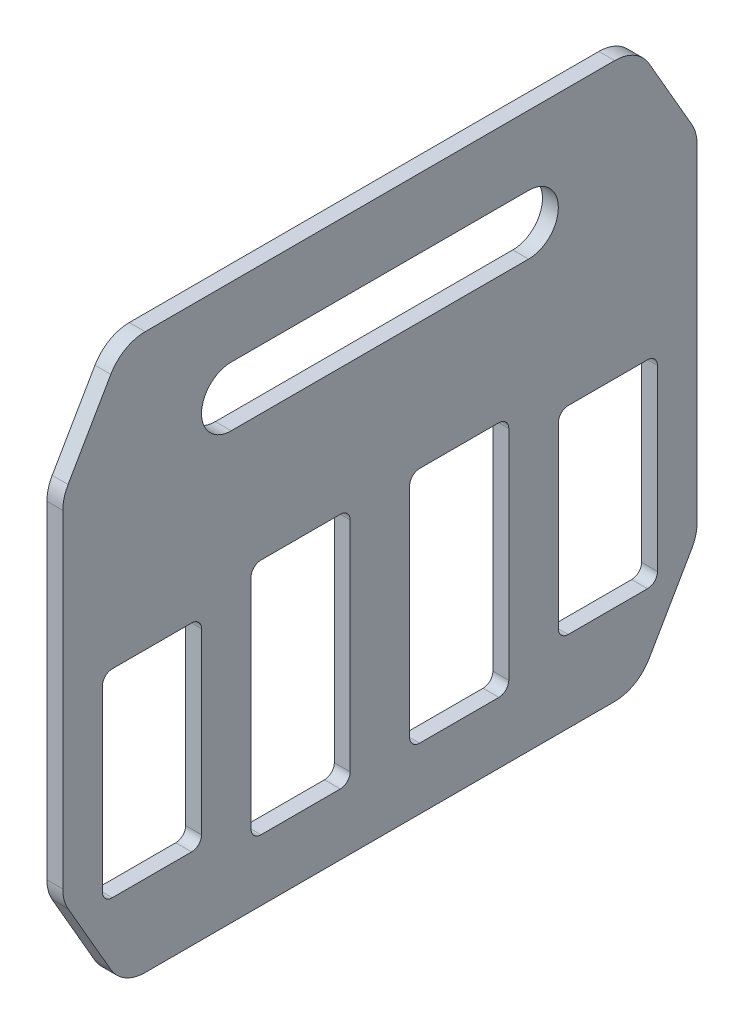
SolidWorks part; units mm, degrees
ref_plane "Front Plane" through (0, 0, 0) normal (0, 0, 1) x (1, 0, 0)
ref_plane "Top Plane" through (0, 0, 0) normal (0, 1, 0) x (1, 0, 0)
ref_plane "Right Plane" through (0, 0, 0) normal (1, 0, 0) x (0, 0, -1)
sketch "Sketch1" plane through (0, 0, 0) normal (1, 0, 0) x (0, 0, -1)
  line L0 (0, 254) -> (0, 0) construction
  line L2 (-203.2, 0) -> (-203.2, 254)
  line L4 (203.2, 0) -> (203.2, 254)
  line L5 (-95.25, 215.9) -> (95.25, 215.9) construction
  line L6 (-95.25, 234.95) -> (95.25, 234.95)
  line L7 (-95.25, 196.85) -> (95.25, 196.85)
  line L8 (-203.2, 127) -> (203.2, 127) construction
  line L15 (203.2, 0) -> (203.2, -76.2)
  line L16 (203.2, -76.2) -> (-203.2, -76.2)
  line L18 (-203.2, 0) -> (-203.2, -76.2)
  line L19 (-203.2, 254) -> (203.2, 254) construction
  line L36 (-203.2, 254) -> (-203.2, 279.4)
  line L37 (-203.2, 279.4) -> (203.2, 279.4)
  line L38 (203.2, 254) -> (203.2, 279.4)
  arc A0 (-95.25, 234.95) -> (-95.25, 196.85) centre (-95.25, 215.9) ccw
  arc A1 (95.25, 196.85) -> (95.25, 234.95) centre (95.25, 215.9) ccw
  point P10 (0, 215.9)
  dimension "D1" = 254
  dimension "D3" = 190.5
  dimension "D4" = 19.05
  dimension "D5" = 38.1
  dimension "D6" = 76.2
  dimension "D7" = 25.4
extrude "Boss-Extrude1" add sketch "Sketch1" along normal blind 10.16
sketch "Sketch2" plane through (0, 0, 0) normal (1, 0, 0) x (0, 0, -1)
  line L14 (-203.2, 127) -> (203.2, 127) construction
  line L15 (-196.85, 132.08) -> (-120.65, 132.08)
  line L16 (-196.85, 132.08) -> (-196.85, 121.92)
  line L17 (-196.85, 121.92) -> (-120.65, 121.92)
  line L18 (-120.65, 132.08) -> (-120.65, 121.92)
  line L19 (-203.2, 0) -> (-203.2, 254) construction
  line L20 (-38.1, 132.08) -> (38.1, 132.08)
  line L21 (-38.1, 132.08) -> (-38.1, 121.92)
  line L22 (38.1, 132.08) -> (38.1, 121.92)
  line L23 (-38.1, 121.92) -> (38.1, 121.92)
  line L24 (120.65, 132.08) -> (196.85, 132.08)
  line L25 (120.65, 132.08) -> (120.65, 121.92)
  line L26 (196.85, 132.08) -> (196.85, 121.92)
  line L27 (120.65, 121.92) -> (196.85, 121.92)
  point P6 (-196.85, 127)
  dimension "D1" = 6.35
  dimension "D2" = 10.16
  dimension "D3" = 76.2
  dimension "D4" = 3
extrude "Cut-Extrude1" cut sketch "Sketch2" along normal blind 4.572
chamfer "Chamfer1" distance 38.1 angle 60 4 edges at (5.08, -76.2, 203.2) (5.08, -76.2, -203.2) (5.08, 279.4, 203.2) (5.08, 279.4, -203.2)
fillet "Fillet1" radius 25.4 8 edges at (5.08, 279.4, -165.1) (5.08, 213.4089, -203.2) (5.08, -10.2089, -203.2) (5.08, -76.2, -165.1) (5.08, -76.2, 165.1) (5.08, -10.2089, 203.2) (5.08, 213.4089, 203.2) (5.08, 279.4, 165.1)
sketch "Sketch4" plane through (0, 0, 0) normal (1, 0, 0) x (0, 0, -1)
  line L11 (0, 279.4) -> (0, -76.2) construction
  line L32 (-203.2, 279.4) -> (203.2, 279.4) construction
  line L33 (203.2, -76.2) -> (-203.2, -76.2) construction
  line L35 (-171.45, 102.87) -> (-120.65, 102.87)
  line L36 (-177.8, 96.52) -> (-177.8, -17.78)
  line L37 (-171.45, -24.13) -> (-120.65, -24.13)
  line L38 (-114.3, 96.52) -> (-114.3, -17.78)
  line L39 (-76.2, 115.57) -> (-25.4, 115.57)
  line L40 (-82.55, 109.22) -> (-82.55, -30.48)
  line L41 (-76.2, -36.83) -> (-25.4, -36.83)
  line L42 (-19.05, 109.22) -> (-19.05, -30.48)
  line L43 (-196.85, 121.92) -> (-120.65, 121.92) construction
  line L44 (19.05, 109.22) -> (19.05, -30.48)
  line L45 (76.2, -36.83) -> (25.4, -36.83)
  line L46 (82.55, 109.22) -> (82.55, -30.48)
  line L47 (76.2, 115.57) -> (25.4, 115.57)
  line L48 (114.3, 96.52) -> (114.3, -17.78)
  line L49 (171.45, -24.13) -> (120.65, -24.13)
  line L50 (177.8, 96.52) -> (177.8, -17.78)
  line L51 (171.45, 102.87) -> (120.65, 102.87)
  arc A16 (-76.2, 115.57) -> (-82.55, 109.22) centre (-76.2, 109.22) ccw
  arc A17 (-25.4, 115.57) -> (-19.05, 109.22) centre (-25.4, 109.22) cw
  arc A18 (-25.4, -36.83) -> (-19.05, -30.48) centre (-25.4, -30.48) ccw
  arc A19 (-82.55, -30.48) -> (-76.2, -36.83) centre (-76.2, -30.48) ccw
  arc A20 (-177.8, -17.78) -> (-171.45, -24.13) centre (-171.45, -17.78) ccw
  arc A21 (-120.65, -24.13) -> (-114.3, -17.78) centre (-120.65, -17.78) ccw
  arc A22 (-120.65, 102.87) -> (-114.3, 96.52) centre (-120.65, 96.52) cw
  arc A23 (-171.45, 102.87) -> (-177.8, 96.52) centre (-171.45, 96.52) ccw
  arc A24 (171.45, 102.87) -> (177.8, 96.52) centre (171.45, 96.52) cw
  arc A25 (120.65, 102.87) -> (114.3, 96.52) centre (120.65, 96.52) ccw
  arc A26 (120.65, -24.13) -> (114.3, -17.78) centre (120.65, -17.78) cw
  arc A27 (177.8, -17.78) -> (171.45, -24.13) centre (171.45, -17.78) cw
  arc A28 (82.55, -30.48) -> (76.2, -36.83) centre (76.2, -30.48) cw
  arc A29 (25.4, -36.83) -> (19.05, -30.48) centre (25.4, -30.48) cw
  arc A30 (25.4, 115.57) -> (19.05, 109.22) centre (25.4, 109.22) ccw
  arc A31 (76.2, 115.57) -> (82.55, 109.22) centre (76.2, 109.22) cw
  point P18 (-82.55, 115.57)
  point P21 (-19.05, 115.57)
  point P26 (-82.55, -36.83)
  point P29 (-177.8, -24.13)
  point P34 (-114.3, 102.87)
  point P37 (-177.8, 102.87)
  point P62 (177.8, 102.87)
  point P63 (114.3, 102.87)
  point P64 (177.8, -24.13)
  point P65 (82.55, -36.83)
  point P66 (19.05, 115.57)
  point P67 (82.55, 115.57)
  dimension "D4" = 152.4
  dimension "D8" = 63.5
  dimension "D9" = 6.35
  dimension "D1" = 6.35
  dimension "D2" = 19.05
  dimension "D3" = 127
  dimension "D5" = 19.05
  dimension "D6" = 63.5
  dimension "D7" = 31.75
extrude "Cut-Extrude2" cut sketch "Sketch4" along normal blind 26.416
